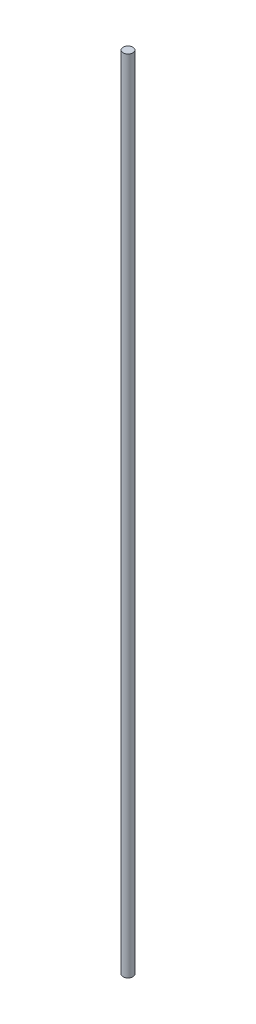
SolidWorks part; units mm, degrees
ref_plane "Front Plane" through (0, 0, 0) normal (0, 0, 1) x (1, 0, 0)
ref_plane "Top Plane" through (0, 0, 0) normal (0, 1, 0) x (1, 0, 0)
ref_plane "Right Plane" through (0, 0, 0) normal (1, 0, 0) x (0, 0, -1)
sketch "Sketch1" plane through (0, 0, 0) normal (0, 1, 0) x (1, 0, 0)
  circle A0 centre (0, 0) radius 1.397
  dimension "D1" = 2.794
extrude "Boss-Extrude1" add sketch "Sketch1" along normal blind 228.6
